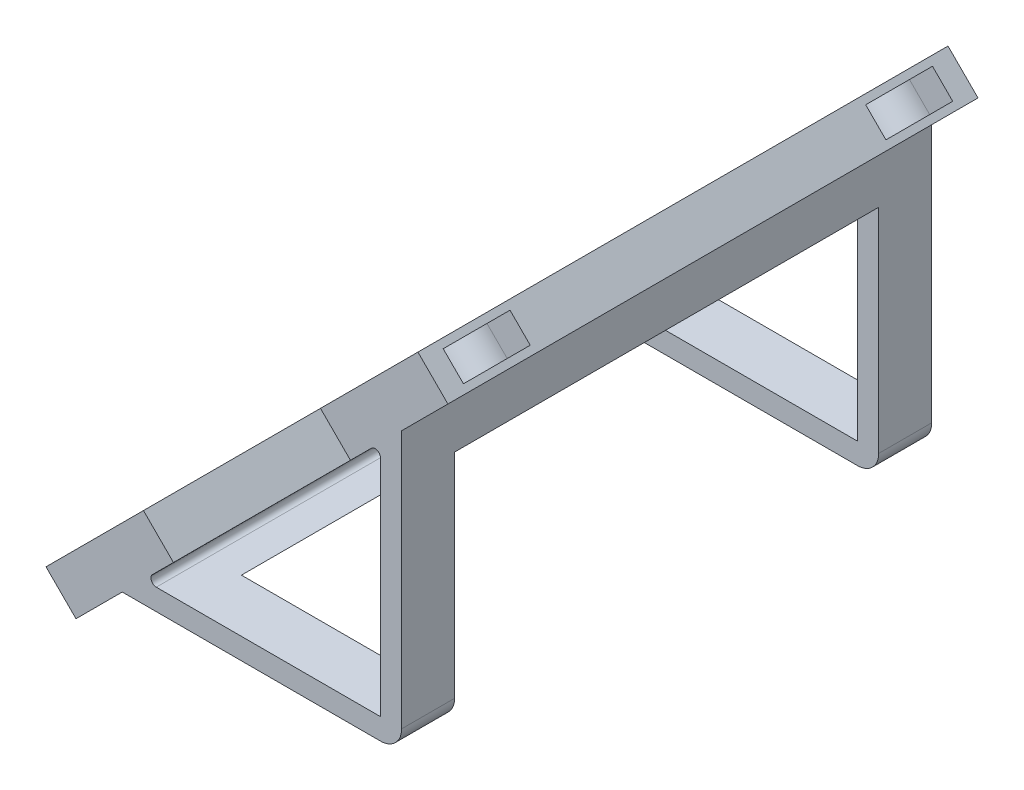
SolidWorks part; units mm, degrees
ref_plane "Front Plane" through (0, 0, 0) normal (0, 0, 1) x (1, 0, 0)
ref_plane "Top Plane" through (0, 0, 0) normal (0, 1, 0) x (1, 0, 0)
ref_plane "Right Plane" through (0, 0, 0) normal (1, 0, 0) x (0, 0, -1)
sketch "Sketch1" plane through (0, 0, 0) normal (0, 0, 1) x (1, 0, 0)
  line L0 (-1.5607, -1) -> (-17.117, 14.5563) construction
  line L9 (-1.5607, 13.0021) -> (0.4393, 13.0021) construction
  line L10 (-23.9142, -1) -> (-1.5607, -1)
  line L11 (-1.5607, -1) -> (-1.5607, 21.3536)
  line L12 (-1.5607, 21.3536) -> (-4.3891, 18.5251)
  line L13 (-4.3891, 18.5251) -> (-7.2175, 21.3536)
  line L14 (-7.2175, 21.3536) -> (1.9749, 30.5459)
  line L15 (0.4393, 23.3536) -> (0.4393, -3)
  line L16 (0.4393, -3) -> (-25.9142, -3)
  line L17 (-33.1066, -4.5355) -> (-23.9142, 4.6569)
  line L18 (-23.9142, 4.6569) -> (-21.0858, 1.8284)
  line L19 (-21.0858, 1.8284) -> (-23.9142, -1)
  line L20 (-1.5607, -1) -> (-17.117, -16.5563) construction
  line L21 (1.9749, 30.5459) -> (4.8033, 27.7175)
  line L22 (4.8033, 27.7175) -> (0.4393, 23.3536)
  line L23 (-27.6658, -3.0731) -> (0.5124, 25.1051) construction
  line L24 (-33.1066, -4.5355) -> (-30.2782, -7.364)
  line L25 (-30.2782, -7.364) -> (-25.9142, -3)
  line L26 (-27.9218, -3.3291) -> (-27.4097, -2.817) construction
  line L27 (-1.8107, -0.75) -> (-1.8107, 19.25) construction
  line L28 (-1.8107, -0.75) -> (-21.8107, -0.75) construction
  line L29 (-1.8107, -0.75) -> (-1.8107, 19.25) construction
  line L30 (-1.8107, -0.75) -> (-21.8107, -0.75) construction
  line L31 (-1.8107, -0.75) -> (-1.5607, -1) construction
  point P4 (-13.5767, 11.016)
  point P27 (-27.6658, -3.0731)
  dimension "D1" = 90
  dimension "D2" = 135
  dimension "D3" = 22
  dimension "D4" = 45
  dimension "D5" = 2
  dimension "D6" = 45
  dimension "D7" = 13
  dimension "D8" = 4
  dimension "D9" = 39.85
  dimension "D10" = 4
  dimension "D11" = 0.5
  dimension "D12" = 0.25
extrude "Boss-Extrude1" add sketch "Sketch1" against normal blind 50
ref_plane "Plane1" through (-12.8713, 12.8713, 0) normal (-0.7071, 0.7071, 0) x (0.7071, 0.7071, 0)
sketch "Sketch2" plane through (-12.8713, 12.8713, 0) normal (-0.7071, 0.7071, 0) x (0.7071, 0.7071, 0)
  line L0 (0, 0) -> (0, 44.925) construction
  line L1 (-19.925, 44.925) -> (19.925, 44.925) construction
  line L2 (-19.925, 44.925) -> (-19.925, 5.075) construction
  line L3 (-19.925, 5.075) -> (19.925, 5.075) construction
  line L4 (19.925, 44.925) -> (19.925, 5.075) construction
  line L6 (-26.617, 50) -> (-26.617, 0) construction
  line L7 (-26.617, 25) -> (-36.617, 25) construction
  line L8 (19.925, 1.925) -> (22.9957, 1.925)
  line L9 (22.9957, 50) -> (22.9957, 0) construction
  line L10 (19.925, 8.225) -> (22.9957, 8.225)
  line L11 (19.925, 41.775) -> (22.9957, 41.775)
  line L12 (19.925, 48.075) -> (22.9957, 48.075)
  line L13 (-19.925, 1.925) -> (-26.617, 1.925)
  line L14 (-19.925, 8.225) -> (-26.617, 8.225)
  line L15 (-19.925, 41.775) -> (-26.617, 41.775)
  line L16 (-19.925, 48.075) -> (-26.617, 48.075)
  line L17 (22.9957, 1.925) -> (22.9957, 8.225)
  line L18 (22.9957, 41.775) -> (22.9957, 48.075)
  line L19 (-26.617, 1.925) -> (-26.617, 8.225)
  line L20 (-26.617, 41.775) -> (-26.617, 48.075)
  arc A0 (-19.925, 41.775) -> (-19.925, 48.075) centre (-19.925, 44.925) ccw
  arc A1 (-19.925, 1.925) -> (-19.925, 8.225) centre (-19.925, 5.075) ccw
  arc A2 (19.925, 48.075) -> (19.925, 41.775) centre (19.925, 44.925) ccw
  arc A3 (19.925, 8.225) -> (19.925, 1.925) centre (19.925, 5.075) ccw
  point P8 (-19.925, 25)
  dimension "D1" = 6.3
  dimension "D3" = 39.85
  dimension "D4" = 10
extrude "Cut-Extrude1" cut sketch "Sketch2" against normal blind 1.35 and the other way blind 1.35
ref_plane "Plane2" through (16.2604, 16.2604, 0) normal (0.7071, 0.7071, 0) x (0, 0, -1)
sketch "Sketch3" plane through (16.2604, 16.2604, 0) normal (0.7071, 0.7071, 0) x (0, 0, -1)
  line L0 (25, 20.2028) -> (25, -9.7972) construction
  line L1 (5, 13.2028) -> (45, 13.2028)
  line L2 (5, 13.2028) -> (5, -6.7972)
  line L3 (5, -6.7972) -> (45, -6.7972)
  line L4 (45, 13.2028) -> (45, -6.7972)
  line L5 (50, 20.2028) -> (0, 20.2028) construction
  line L6 (50, 16.2028) -> (0, 16.2028) construction
  point P9 (25, 13.2028)
  dimension "D1" = 30
  dimension "D2" = 3
  dimension "D3" = 20
  dimension "D4" = 40
extrude "Cut-Extrude2" cut sketch "Sketch3" against normal through all
fillet "Fillet1" radius 0.5 2 edges at (-1.5607, 21.3536, -25) (-23.9142, -1, -25)
fillet "Fillet2" radius 2 2 edges at (0.4393, -3, -2.5) (0.4393, -3, -47.5)
